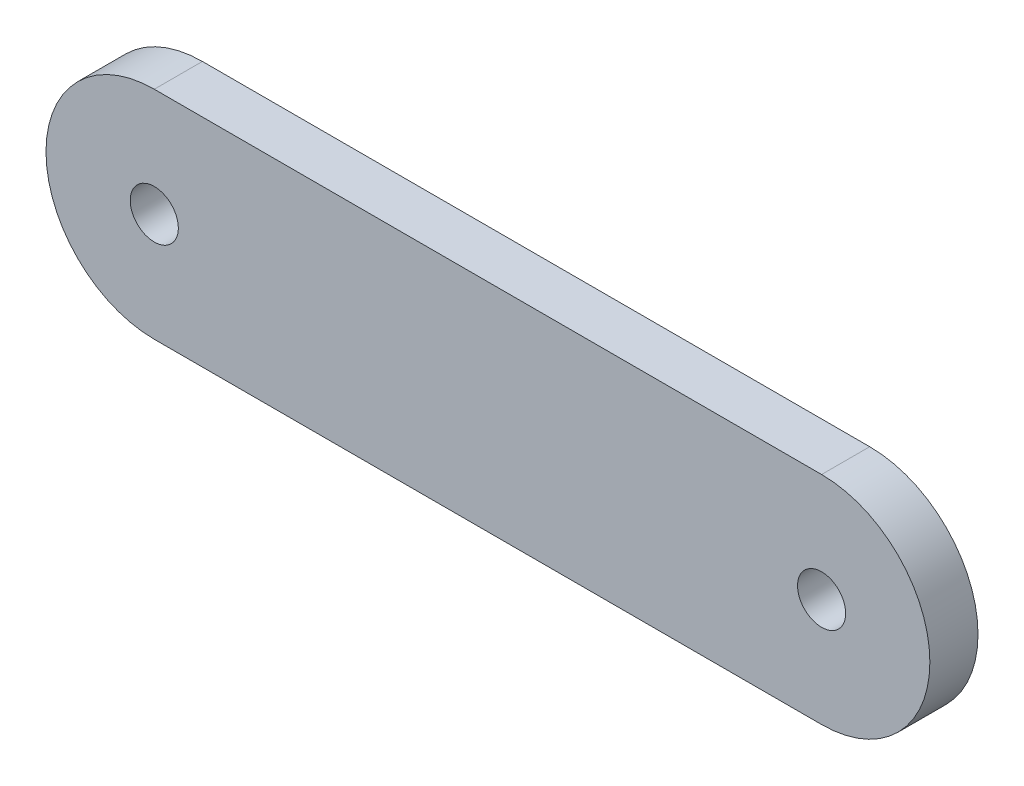
SolidWorks part; units mm, degrees
ref_plane "Front Plane" through (0, 0, 0) normal (0, 0, 1) x (1, 0, 0)
ref_plane "Top Plane" through (0, 0, 0) normal (0, 1, 0) x (1, 0, 0)
ref_plane "Right Plane" through (0, 0, 0) normal (1, 0, 0) x (0, 0, -1)
sketch "Sketch1" plane through (0, 0, 0) normal (0, 0, 1) x (1, 0, 0)
  line L1 (2.2495, 2.25) -> (16.1156, 2.25)
  line L2 (2.2495, -2.25) -> (16.1156, -2.25)
  arc A2 (2.2495, 2.25) -> (2.2495, -2.25) centre (2.2495, 0) ccw
  arc A3 (16.1156, -2.25) -> (16.1156, 2.25) centre (16.1156, 0) ccw
  circle A4 centre (2.2495, 0) radius 0.5
  circle A5 centre (16.1156, 0) radius 0.5
  dimension "D1" = 4.5
extrude "Boss-Extrude1" add sketch "Sketch1" along normal blind 1
